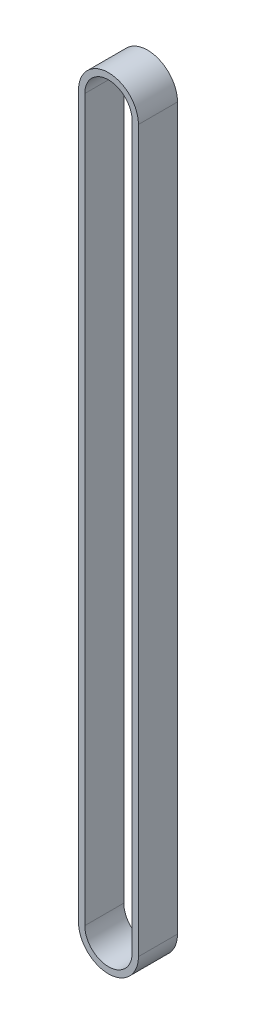
SolidWorks part; units mm, degrees
ref_plane "Front Plane" through (0, 0, 0) normal (0, 0, 1) x (1, 0, 0)
ref_plane "Top Plane" through (0, 0, 0) normal (0, 1, 0) x (1, 0, 0)
ref_plane "Right Plane" through (0, 0, 0) normal (1, 0, 0) x (0, 0, -1)
sketch "Sketch1" plane through (0, 0, 0) normal (0, 0, 1) x (1, 0, 0)
  line L0 (0, 201.1533) -> (0, -75.6367) construction
  line L1 (9.105, 201.1533) -> (9.105, -75.6367)
  line L2 (-9.105, 201.1533) -> (-9.105, -75.6367)
  line L3 (11.505, 201.1533) -> (11.505, -75.6367)
  line L4 (-11.505, 201.1533) -> (-11.505, -75.6367)
  arc A0 (9.105, 201.1533) -> (-9.105, 201.1533) centre (0, 201.1533) ccw
  arc A1 (-9.105, -75.6367) -> (9.105, -75.6367) centre (0, -75.6367) ccw
  arc A2 (-11.505, -75.6367) -> (11.505, -75.6367) centre (0, -75.6367) ccw
  arc A3 (11.505, 201.1533) -> (-11.505, 201.1533) centre (0, 201.1533) ccw
  point P3 (0, 62.7583)
  dimension "D1" = 295
  dimension "D2" = 18.21
  dimension "D3" = 2.4
extrude "Boss-Extrude1" add sketch "Sketch1" along normal mid plane 15
